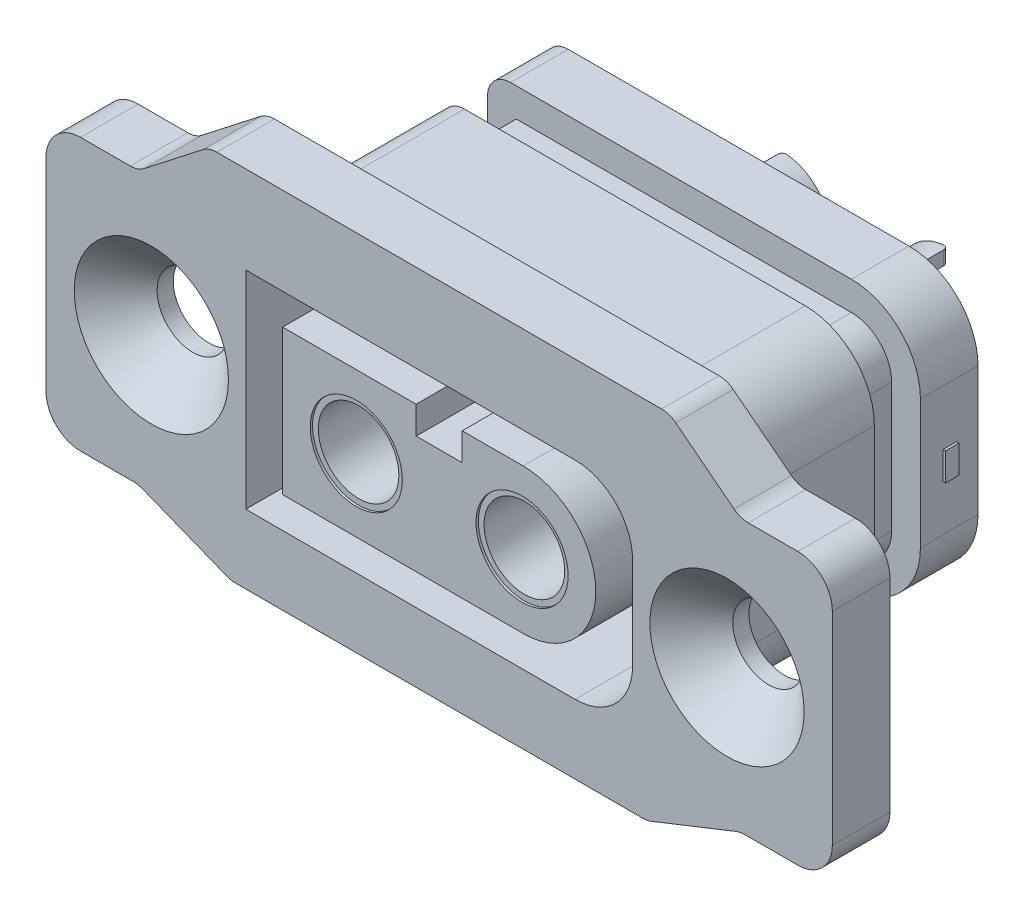
SolidWorks part; units mm, degrees
ref_plane "Front Plane" through (0, 0, 0) normal (0, 0, 1) x (1, 0, 0)
ref_plane "Top Plane" through (0, 0, 0) normal (0, 1, 0) x (1, 0, 0)
ref_plane "Right Plane" through (0, 0, 0) normal (1, 0, 0) x (0, 0, -1)
sketch "Sketch1" plane through (0, 0, 0) normal (0, 0, 1) x (1, 0, 0)
  line L1 (9.4, -5.8) -> (-9.4, -5.8)
  line L2 (9.4, -5.8) -> (9.4, 5.8)
  line L3 (9.4, 5.8) -> (-9.4, 5.8)
  line L4 (-9.4, -5.8) -> (-9.4, 5.8)
  line L5 (9.4, -5.8) -> (-9.4, 5.8) construction
  line L6 (9.4, 5.8) -> (-9.4, -5.8) construction
  point P0 (0, 0)
  dimension "D1" = 18.8
  dimension "D2" = 11.6
extrude "Boss-Extrude1" add sketch "Sketch1" against normal blind 11.5
sketch "Sketch2" plane through (0, 0, 0) normal (0, 0, 1) x (1, 0, 0)
  line L1 (17.075, -5.9) -> (-17.075, -5.9)
  line L2 (17.075, -5.9) -> (17.075, 5.9)
  line L3 (17.075, 5.9) -> (-17.075, 5.9)
  line L4 (-17.075, -5.9) -> (-17.075, 5.9)
  line L5 (17.075, -5.9) -> (-17.075, 5.9) construction
  line L6 (17.075, 5.9) -> (-17.075, -5.9) construction
  point P0 (0, 0)
  dimension "D1" = 11.8
  dimension "D2" = 34.15
extrude "Boss-Extrude2" add sketch "Sketch2" along normal blind 2.5
sketch "Sketch3" plane through (0, 0, 0) normal (0, 0, 1) x (1, 0, 0)
  line L0 (-10, 8.3) -> (-13.075, 5.9)
  line L1 (9.0361, -7.5) -> (-9.0361, -7.5)
  line L3 (10, 8.3) -> (-10, 8.3)
  line L5 (9.0361, -7.5) -> (-10, 8.3) construction
  line L6 (10, 8.3) -> (-9.0361, -7.5) construction
  line L7 (17.075, 5.9) -> (-17.075, 5.9) construction
  line L8 (-17.075, 5.9) -> (-17.075, -5.9) construction
  line L9 (-13.075, 5.9) -> (-13.075, -5.9)
  line L10 (-17.075, -5.9) -> (17.075, -5.9) construction
  line L11 (-13.075, -5.9) -> (-9.0361, -7.5)
  line L12 (9.0361, -7.5) -> (13.075, -5.9)
  line L13 (13.075, -5.9) -> (13.075, 5.9)
  line L14 (13.075, 5.9) -> (10, 8.3)
  line L15 (17.075, -5.9) -> (17.075, 5.9) construction
  point P0 (0, 0)
  dimension "D1" = 15.8
  dimension "D2" = 20
  dimension "D3" = 4
  dimension "D4" = 4
  dimension "D5" = 10
extrude "Boss-Extrude3" add sketch "Sketch3" along normal up to surface (2.5 mm away) up to face at (0, 0, 2.5)
fillet "Fillet1" radius 1.5 4 edges at (17.075, -5.9, 1.25) (17.075, 5.9, 1.25) (-17.075, -5.9, 1.25) (-17.075, 5.9, 1.25)
fillet "Fillet2" radius 1 8 edges at (-9.0361, -7.5, 1.25) (9.0361, -7.5, 1.25) (10, 8.3, 1.25) (-10, 8.3, 1.25) (-13.075, -5.9, 1.25) (13.075, -5.9, 1.25) (13.075, 5.9, 1.25) (-13.075, 5.9, 1.25)
hole_wizard "CSK for M3 Hex Socket Countersunk Head Screw1" positions "Sketch4" profile "Sketch5" countersink size "M3" standard "DIN" end condition through all
sketch "Sketch4" plane through (0, 0, 2.5) normal (0, 0, 1) x (1, 0, 0)
  point P0 (-12.5, 0)
  point P2 (12.5, 0)
  dimension "D1" = 25
  dimension "D2" = 12.5
sketch "Sketch5" plane through (-12.5, 0, 2.5) normal (1, 0, 0) x (0, -1, 0)
  line L0 (0, 0) -> (0, 14)
  line L1 (0, 14) -> (1.55, 14)
  line L2 (1.55, 14) -> (1.55, 1.8)
  line L3 (1.55, 1.8) -> (3.35, 0)
  line L5 (3.35, 0) -> (0, 0)
  line L6 (-1.55, 1.8) -> (-3.35, 0) construction
  line L11 (0, -6.35) -> (0, 107.95) construction
  dimension "Thru Hole Dia." = 3.1
  dimension "Thru Hole Depth" = 14
  dimension "Near C'Sink Dia." = 6.7
  dimension "Near C'Sink Angle" = 90
fillet "Fillet3" radius 3 2 edges at (9.4, -5.8, -5.75) (9.4, 5.8, -5.75)
fillet "Fillet4" radius 1 2 edges at (-9.4, -5.8, -5.75) (-9.4, 5.8, -5.75)
ref_plane "Plane1" through (0, 0, -7) normal (0, 0, -1) x (-1, 0, 0)
sketch "Sketch6" plane through (0, 0, -7) normal (0, 0, -1) x (-1, 0, 0)
  line L8 (-6.4, -4.55) -> (8.15, -4.55)
  line L9 (8.15, -4.55) -> (8.15, 4.55)
  line L10 (8.15, 4.55) -> (-6.4, 4.55)
  line L11 (-8.15, 2.8) -> (-8.15, -2.8)
  line L12 (-6.4, -4.55) -> (8.15, -4.55)
  line L13 (8.15, -4.55) -> (8.15, 4.55)
  line L14 (8.15, 4.55) -> (-6.4, 4.55)
  line L15 (-8.15, 2.8) -> (-8.15, -2.8)
  line L16 (-6.4, -6.7) -> (8.4, -6.7)
  line L17 (10.3, -4.8) -> (10.3, 4.8)
  line L18 (8.4, 6.7) -> (-6.4, 6.7)
  line L19 (-10.3, 2.8) -> (-10.3, -2.8)
  line L20 (-6.4, -6.7) -> (8.4, -6.7)
  line L21 (10.3, -4.8) -> (10.3, 4.8)
  line L22 (8.4, 6.7) -> (-6.4, 6.7)
  line L23 (-10.3, 2.8) -> (-10.3, -2.8)
  arc A10 (-6.4, 4.55) -> (-8.15, 2.8) centre (-6.4, 2.8) ccw
  arc A11 (-8.15, -2.8) -> (-6.4, -4.55) centre (-6.4, -2.8) ccw
  arc A14 (-6.4, 4.55) -> (-8.15, 2.8) centre (-6.4, 2.8) ccw
  arc A15 (-8.15, -2.8) -> (-6.4, -4.55) centre (-6.4, -2.8) ccw
  arc A16 (8.4, -6.7) -> (10.3, -4.8) centre (8.4, -4.8) ccw
  arc A17 (10.3, 4.8) -> (8.4, 6.7) centre (8.4, 4.8) ccw
  arc A18 (-6.4, 6.7) -> (-10.3, 2.8) centre (-6.4, 2.8) ccw
  arc A19 (-10.3, -2.8) -> (-6.4, -6.7) centre (-6.4, -2.8) ccw
  arc A20 (8.4, -6.7) -> (10.3, -4.8) centre (8.4, -4.8) ccw
  arc A21 (10.3, 4.8) -> (8.4, 6.7) centre (8.4, 4.8) ccw
  arc A22 (-6.4, 6.7) -> (-10.3, 2.8) centre (-6.4, 2.8) ccw
  arc A23 (-10.3, -2.8) -> (-6.4, -6.7) centre (-6.4, -2.8) ccw
  dimension "D1" = 1.25
  dimension "D2" = 0.9
extrude "Cut-Extrude1" cut sketch "Sketch6" along normal blind 2
sketch "Sketch7" plane through (0, 0, -11.5) normal (0, 0, -1) x (-1, 0, 0)
  line L0 (-0.3, 3.1) -> (-6.7, 3.1)
  line L1 (-6.7, 3.1) -> (-6.7, -3.1)
  line L2 (-6.7, -3.1) -> (-0.3, -3.1)
  line L3 (-9.4, -2.8) -> (-9.4, 2.8) construction
  line L6 (0.3, -3.1) -> (0.3, 3.1)
  line L8 (-6.4, -3.1) -> (6.7, -3.1)
  line L9 (6.7, -3.1) -> (6.7, 3.1)
  line L10 (6.7, 3.1) -> (-6.4, 3.1)
  line L11 (-6.7, 2.8) -> (-6.7, -2.8)
  line L13 (6.7, -3.1) -> (6.7, 3.1)
  line L14 (6.7, 3.1) -> (0.3, 3.1)
  line L16 (-0.3, -3.1) -> (-0.3, 3.1)
  line L17 (0.3, -3.1) -> (-0.3, 3.1) construction
  line L18 (0.3, 3.1) -> (-0.3, -3.1) construction
  line L19 (0.3, -3.1) -> (6.7, -3.1)
  arc A8 (-6.4, 3.1) -> (-6.7, 2.8) centre (-6.4, 2.8) ccw
  arc A9 (-6.7, -2.8) -> (-6.4, -3.1) centre (-6.4, -2.8) ccw
  point P0 (0, 0)
  dimension "D2" = 0.6
  dimension "D3" = 2.7
  dimension "D1" = 2.7
extrude "Cut-Extrude2" cut sketch "Sketch7" against normal blind 2
fillet "Fillet5" radius 1.5 2 edges at (6.7, -3.1, -10.5) (6.7, 3.1, -10.5)
sketch "Sketch8" plane through (0, 0, -9.5) normal (0, 0, -1) x (-1, 0, 0)
  circle A0 centre (-3.6, 0) radius 2.1
  circle A1 centre (3.6, 0) radius 2.1
  dimension "D1" = 4.2
  dimension "D2" = 4.2
  dimension "D3" = 7.2
  dimension "D4" = 3.6
extrude "Boss-Extrude4" add sketch "Sketch8" along normal blind 6.5
hole_wizard "Ø3.0mm Dowel Hole1" positions "Sketch9" profile "Sketch10" hole size "Ø3.0" standard "DIN"
sketch "Sketch9" plane through (0, 0, -16) normal (0, 0, -1) x (-1, 0, 0)
  point P0 (-3.6, 0)
  point P3 (3.6, 0)
sketch "Sketch10" plane through (3.6, 0, -16) normal (1, 0, 0) x (0, 1, 0)
  line L0 (0, 0) -> (0, 4.2013)
  line L1 (0, 4.2013) -> (1.5, 3.3)
  line L2 (1.5, 3.3) -> (1.5, 0)
  line L5 (1.5, 0) -> (0, 0)
  line L10 (0, 4.2013) -> (-1.5, 3.3) construction
  line L11 (0, -6.35) -> (0, 107.95) construction
  dimension "Hole Dia." = 3
  dimension "Hole Depth" = 3.3
  dimension "Drill Angle" = 118
sketch "Sketch11" plane through (0, 0, 0) normal (0, 1, 0) x (1, 0, 0)
  line L0 (-5.7, 16) -> (-5.7, 9.5) construction
  line L1 (-3.6, 13) -> (-6.9923, 13)
  line L2 (-3.6, 13) -> (-3.6, 17.3313)
  line L3 (-3.6, 17.3313) -> (-6.9923, 17.3313)
  line L4 (-6.9923, 13) -> (-6.9923, 17.3313)
  line L5 (3.6, 13) -> (6.3563, 13)
  line L6 (3.6, 13) -> (3.6, 18.3354)
  line L7 (3.6, 18.3354) -> (6.3563, 18.3354)
  line L8 (6.3563, 13) -> (6.3563, 18.3354)
  line L9 (5.7, 9.5) -> (5.7, 16) construction
  line L10 (5.7, 16) -> (1.5, 16) construction
  line L11 (-1.5, 16) -> (-5.7, 16) construction
  dimension "D1" = 2.1
  dimension "D2" = 2.1
  dimension "D3" = 3
  dimension "D4" = 3
extrude "Cut-Extrude3" cut sketch "Sketch11" against normal mid plane 6.5
fillet "Fillet6" radius 0.2 8 edges at (3.6, -1.8, -13) (3.6, 1.8, -13) (3.6, -1.8, -16) (3.6, 1.8, -16) (-3.6, 1.8, -16) (-3.6, -1.8, -16) (-3.6, 1.8, -13) (-3.6, -1.8, -13)
sketch "Sketch12" plane through (0, 0, 2.5) normal (0, 0, 1) x (1, 0, 0)
  line L0 (3.65, -3.15) -> (-6.8, -3.15)
  line L1 (5.9, -4.5) -> (-8.4, -4.5)
  line L2 (8.4, -2) -> (8.4, 2)
  line L4 (-8.4, -4.5) -> (-8.4, 4.5)
  line L5 (8.4, -4.5) -> (-8.4, 4.5) construction
  line L6 (8.4, 4.5) -> (-8.4, -4.5) construction
  line L9 (3.65, 3.15) -> (1, 3.15)
  line L10 (-6.8, -3.15) -> (-6.8, 3.15)
  line L11 (5.5014, -2.5485) -> (-6.8, 3.15) construction
  line L12 (5.5014, 2.5485) -> (-6.8, -3.15) construction
  line L13 (-1, 3.15) -> (-6.8, 3.15)
  line L15 (1, 3.15) -> (1, 1.95)
  line L16 (1, 1.95) -> (-1, 1.95)
  line L17 (-1, 3.15) -> (-1, 1.95)
  line L18 (0, 3.15) -> (-1, 1.95) construction
  line L19 (1, 1.95) -> (0, 3.15) construction
  line L20 (-8.4, 4.5) -> (5.9, 4.5)
  arc A0 (5.9, -4.5) -> (8.4, -2) centre (5.9, -2) ccw
  arc A1 (8.4, 2) -> (5.9, 4.5) centre (5.9, 2) ccw
  arc A2 (3.65, 3.15) -> (3.65, -3.15) centre (3.65, 0) cw
  point P0 (0, 0)
  point P12 (0, 0)
  point P15 (0, 3.15)
  dimension "D3" = 2.5
  dimension "D1" = 9
  dimension "D2" = 16.8
  dimension "D4" = 6.3
  dimension "D5" = 13.6
  dimension "D6" = 2
  dimension "D7" = 0
  dimension "D8" = 1.2
extrude "Cut-Extrude6" cut sketch "Sketch12" against normal blind 8.8
sketch "Sketch13" plane through (0, 0, 2.5) normal (0, 0, 1) x (1, 0, 0)
  circle A0 centre (-3.6, 0) radius 2
  circle A1 centre (3.6, 0) radius 2
  dimension "D1" = 7.2
  dimension "D3" = 4
  dimension "D4" = 4
  dimension "D2" = 3.6
extrude "Cut-Extrude7" cut sketch "Sketch13" against normal blind 0.1
sketch "Sketch14" plane through (0, 0, 2.5) normal (0, 0, 1) x (1, 0, 0)
  circle A0 centre (-3.6, 0) radius 1.75
  circle A1 centre (3.6, 0) radius 1.75
  dimension "D1" = 3.5
  dimension "D2" = 3.5
extrude "Cut-Extrude8" cut sketch "Sketch14" against normal blind 12
sketch "Sketch15" plane through (9.4, 0, 0) normal (1, 0, 0) x (0, 0, -1)
  line L0 (9, 2.8) -> (9, -2.8) construction
  text T0 "<b>-</b>" font "Century Gothic" height 3.5
extrude "Boss-Extrude5" add sketch "Sketch15" along normal blind 0.1
sketch "Sketch16" plane through (-9.4, 0, 0) normal (-1, 0, 0) x (0, 0, 1)
  line L0 (-8.5857, -4.55) -> (-8.5857, 4.55) construction
  line L1 (-9, -4.55) -> (-7, -4.55) construction
  line L2 (-9, 4.55) -> (-7, 4.55) construction
  text T0 "<b>+</b>" font "Century Gothic" height 3.5
extrude "Boss-Extrude6" add sketch "Sketch16" along normal blind 0.1
